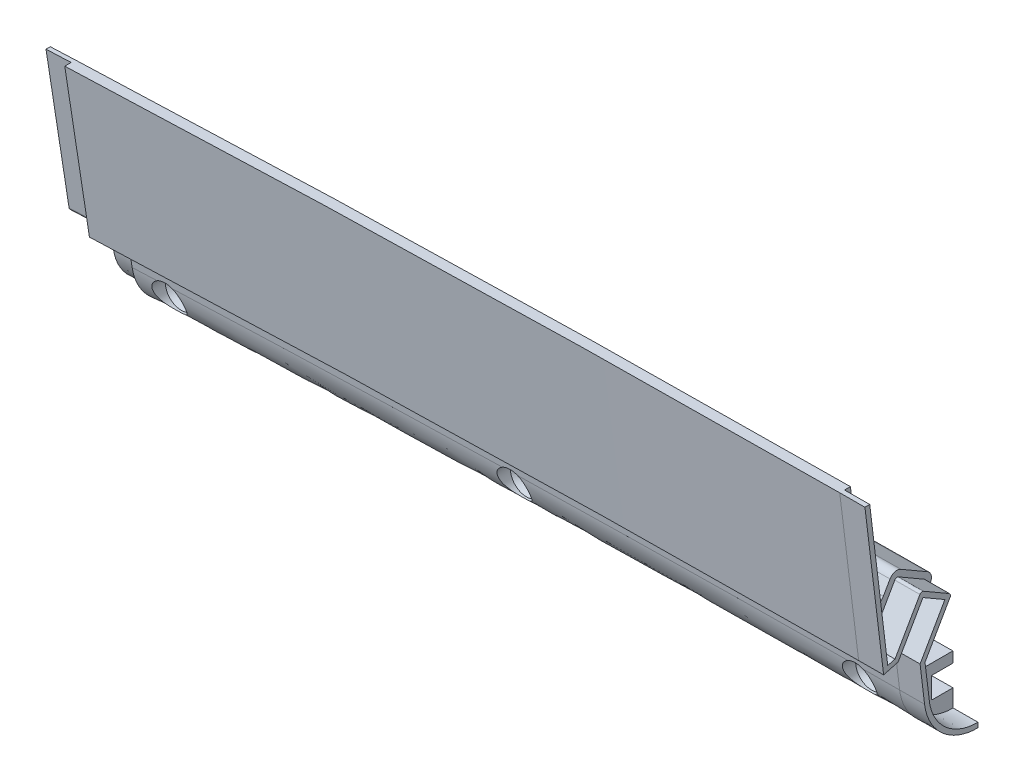
SolidWorks part; units mm, degrees
ref_plane "Front Plane" through (0, 0, 0) normal (0, 0, 1) x (1, 0, 0)
ref_plane "Top Plane" through (0, 0, 0) normal (0, 1, 0) x (1, 0, 0)
ref_plane "Right Plane" through (0, 0, 0) normal (1, 0, 0) x (0, 0, -1)
ref_plane "Plane3" through (-117.056, -3.871, 0) normal (0.9995, 0.0331, 0) x (0, 0, -1)
sketch "Sketch2" plane through (-117.056, -3.871, 0) normal (0.9995, 0.0331, 0) x (0, 0, -1)
  line L0 (-101.6, -41.1511) -> (-101.6, -45.9265)
  line L1 (-101.6, -41.1511) -> (-101.6, -45.9265)
  line L2 (-106.68, -45.9265) -> (-106.68, -50.6257)
  line L3 (-106.68, -45.9265) -> (-106.68, -50.6257)
  line L4 (-101.6, -50.6257) -> (-106.68, -50.6257)
  line L5 (-101.6, -50.6257) -> (-106.68, -50.6257)
  line L6 (-101.6, -50.6257) -> (-101.6, -56.1377)
  line L7 (-101.6, -50.6257) -> (-101.6, -56.1377)
  line L8 (-106.68, -45.9265) -> (-101.6, -45.9265)
  line L9 (-106.68, -45.9265) -> (-101.6, -45.9265)
  line L10 (-106.8705, -50.8162) -> (-108.9961, -53.9781) construction
  line L11 (-101.7905, -43.196) -> (-101.7905, -45.736)
  line L12 (-106.8705, -45.736) -> (-101.7905, -45.736)
  line L13 (-106.8705, -45.736) -> (-106.8705, -50.8162)
  line L14 (-101.7905, -50.8162) -> (-106.8705, -50.8162)
  line L15 (-101.7905, -50.8162) -> (-101.7905, -56.1377)
  line L16 (-101.7905, -43.196) -> (-101.6, -43.196)
  line L17 (-101.7905, -41.1511) -> (-101.7905, -45.736) construction
  line L18 (-120.8053, -33.0481) -> (-115.57, -36.0708)
  line L19 (-120.8053, -33.0481) -> (-115.57, -36.0708)
  line L20 (-109.601, -25.7318) -> (-114.8363, -22.709)
  line L21 (-109.601, -25.7318) -> (-114.8363, -22.709)
  line L22 (-114.8363, -22.709) -> (-120.8053, -33.0481)
  line L23 (-114.8363, -22.709) -> (-120.8053, -33.0481)
  line L24 (-115.57, -36.0708) -> (-109.601, -25.7318)
  line L25 (-115.57, -36.0708) -> (-109.601, -25.7318)
  line L26 (-115.57, -36.0708) -> (-114.523, -44.9291)
  line L28 (-118.1876, -34.5595) -> (-112.2186, -24.2204) construction
  line L29 (-114.6403, -39.5406) -> (-107.0838, -26.4518)
  line L30 (-107.7811, -23.8496) -> (-114.1162, -20.1918)
  line L31 (-116.7185, -20.8891) -> (-124.2749, -33.9778)
  line L33 (-106.1314, -24.8021) -> (-115.766, -19.2393) construction
  line L34 (-115.766, -19.2393) -> (-124.2749, -33.9778) construction
  line L35 (-114.6403, -39.5406) -> (-106.1314, -24.8021) construction
  line L36 (-124.2749, -33.9778) -> (-114.6403, -39.5406) construction
  line L37 (-112.9486, -36.6103) -> (-112.1701, -43.196)
  line L38 (-124.2749, -33.9778) -> (-128.0422, -2.1051)
  line L39 (-128.0422, -2.1051) -> (-132.6063, -0.4439)
  line L40 (-50.8, 0.7495) -> (-2184.4, 0.7495)
  line L41 (-125.822, 0.7495) -> (-133.442, 0.7495)
  line L42 (-122.1519, -30.3004) -> (-125.822, 0.7495)
  arc A0 (-114.523, -44.9291) -> (-101.7905, -56.1377) centre (-101.9108, -43.4383) ccw
  arc A2 (-114.1162, -20.1918) -> (-116.7185, -20.8891) centre (-115.0687, -21.8416) ccw
  arc A3 (-107.0838, -26.4518) -> (-107.7811, -23.8496) centre (-108.7336, -25.4993) ccw
  arc A4 (-133.442, 0.7495) -> (-132.6063, -0.4439) centre (-132.172, 0.7495) ccw
  point P41 (-133.442, 0.7495)
  dimension "D2" = 25.4
  dimension "D6" = 1.905
  dimension "D8" = 2.54
  dimension "D4" = 2.54
  dimension "D5" = 2.54
  dimension "D7" = 2.54
  dimension "D9" = 2.54
  dimension "D10" = 20
  dimension "D11" = 7.62
  dimension "D12" = 3.81
  dimension "D3" = 0.1905
sketch "Sketch3" plane through (0, 0, 101.6) normal (0, 0, 1) x (1, 0, 0)
  arc A0 (622.1039, -83.1998) -> (-622.1039, -83.1998) centre (0, -4954.4862) ccw construction
  arc A1 (622.1039, -83.1998) -> (-622.1039, -83.1998) centre (0, -4954.4862) ccw
sketch "Sketch4" plane through (-117.3306, 4.4304, 1117.6) normal (0.9995, 0.0331, 0) x (0, 0, -1)
  line L29 (1009.8189, -32.1556) -> (1003.4838, -28.4978) construction
  line L32 (1000.8815, -29.1951) -> (993.3251, -42.2838) construction
  line L35 (993.3251, -42.2838) -> (989.5578, -10.4111) construction
  line L50 (995.4481, -38.6064) -> (991.778, -7.5565) construction
  line L51 (1002.03, -44.3768) -> (1003.077, -53.235) construction
  line L52 (1015.8095, -59.1222) -> (1015.8095, -64.4437) construction
  line L53 (1015.8095, -59.1222) -> (1010.7295, -59.1222) construction
  line L54 (1010.7295, -54.042) -> (1010.7295, -59.1222) construction
  line L55 (1010.7295, -54.042) -> (1015.8095, -54.042) construction
  line L56 (1015.8095, -51.502) -> (1015.8095, -54.042) construction
  line L57 (1015.8095, -51.502) -> (1016, -51.502) construction
  line L58 (1004.6514, -44.9163) -> (1005.4299, -51.502) construction
  line L60 (1002.7637, -31.015) -> (996.7947, -41.3541) construction
  line L61 (1007.999, -34.0377) -> (1002.7637, -31.015) construction
  line L62 (1002.03, -44.3768) -> (1007.999, -34.0377) construction
  line L64 (991.5295, -5.4538) -> (988.9718, -5.4538)
  line L69 (1009.8189, -32.1556) -> (1003.4838, -28.4978)
  line L70 (1000.8815, -29.1951) -> (999.2724, -31.9822)
  line L71 (993.3251, -42.2838) -> (988.9718, -5.4538)
  line L74 (994.5502, -31.0104) -> (991.5295, -5.4538)
  line L75 (1002.03, -44.3768) -> (1003.077, -53.235)
  line L76 (1015.8095, -59.1222) -> (1015.8095, -64.4437)
  line L77 (1015.8095, -59.1222) -> (1010.7295, -59.1222)
  line L78 (1010.7295, -54.042) -> (1010.7295, -59.1222)
  line L79 (1010.7295, -54.042) -> (1015.8095, -54.042)
  line L80 (1015.8095, -51.502) -> (1015.8095, -54.042)
  line L81 (1015.8095, -51.502) -> (1007.6873, -51.502)
  line L82 (1004.7505, -45.7539) -> (1005.1649, -49.2601)
  line L84 (1002.7637, -31.015) -> (996.7947, -41.3541)
  line L85 (1007.999, -34.0377) -> (1002.7637, -31.015)
  line L86 (1002.03, -44.3768) -> (1007.999, -34.0377)
  line L87 (996.7947, -41.3541) -> (993.3251, -42.2838)
  line L88 (1005.0732, -44.1858) -> (1010.5162, -34.7578)
  arc A8 (1010.5162, -34.7578) -> (1009.8189, -32.1556) centre (1008.8664, -33.8053) ccw construction
  arc A9 (1003.4838, -28.4978) -> (1000.8815, -29.1951) centre (1002.5313, -30.1476) ccw construction
  arc A11 (1003.077, -53.235) -> (1015.8095, -64.4437) centre (1015.6892, -51.7443) ccw construction
  arc A12 (1010.5162, -34.7578) -> (1009.8189, -32.1556) centre (1008.8664, -33.8053) ccw
  arc A13 (1003.4838, -28.4978) -> (1000.8815, -29.1951) centre (1002.5313, -30.1476) ccw
  arc A15 (1003.077, -53.235) -> (1015.8095, -64.4437) centre (1015.6892, -51.7443) ccw
  arc A16 (1005.1649, -49.2601) -> (1007.6873, -51.502) centre (1007.6873, -48.962) ccw
  arc A17 (1004.7505, -45.7539) -> (1005.0732, -44.1858) centre (1007.2729, -45.4558) cw
  arc A18 (994.5502, -31.0104) -> (999.2724, -31.9822) centre (997.0727, -30.7122) ccw
  dimension "D2" = 2.54
  dimension "D1" = 36.83
sweep "Sweep3" add profiles "Sketch4" path "Sketch3"
sketch "Sketch5" plane through (0, 0, 101.7905) normal (0, 0, -1) x (-1, 0, 0)
  line L0 (207.2142, -20.037) -> (0, -4954.4862) construction
  line L1 (0, -4954.4862) -> (22.6014, 0.3132) construction
  line L2 (117.0808, -1.0187) -> (0, -4954.4862) construction
  arc A1 (628.0925, -39.606) -> (-627.2635, -39.5001) centre (0, -4954.4862) ccw construction
  point P2 (0, 0)
  point P4 (206.8956, -9.432)
  point P16 (117.0808, -1.0187)
ref_plane "Plane1" through (-207.6894, -8.7216, 0) normal (-0.9991, -0.042, 0) x (0.042, -0.9991, 0)
ref_plane "Plane2" through (-22.5995, -0.1031, 0) normal (1, 0.0046, 0) x (-0.0046, 1, 0)
other "SurfaceCut1"
other "SurfaceCut2"
sketch "Sketch8" plane through (-117.056, -3.871, 0) normal (0.9995, 0.0331, 0) x (0, 0, -1)
  line L0 (-106.8705, -50.8162) -> (-106.8705, -45.736)
  line L1 (-106.8705, -50.8162) -> (-106.8705, -45.736)
  line L2 (-106.8705, -48.2761) -> (-119.5705, -48.2761)
  line L3 (-119.5705, -48.2761) -> (-119.5705, -44.4661)
  line L4 (-119.5705, -44.4661) -> (-110.6805, -44.4661)
  line L5 (-110.6805, -44.4661) -> (-108.7755, -46.3711)
  line L6 (-108.7755, -46.3711) -> (-106.8705, -46.3711)
  line L7 (-119.5705, -48.2761) -> (-117.7248, -48.2761) construction
  dimension "D1" = 1.905
  dimension "D2" = 1.905
  dimension "D3" = 12.7
  dimension "D4" = 45
  dimension "D5" = 3.81
revolve "Cut-Revolve1" cut sketch "Sketch8" angle 360 about L7
sketch "Sketch9" plane through (0, 0, 106.8705) normal (0, 0, -1) x (-1, 0, 0)
  line L0 (198.0737, -52.2212) -> (197.8686, -57.297) construction
  line L1 (32.934, -48.3318) -> (32.8999, -53.4117) construction
  arc A1 (205.8492, -52.5415) -> (22.3798, -48.2723) centre (0, -4954.4862) ccw construction
  arc A2 (205.6361, -57.617) -> (22.3566, -53.3522) centre (0, -4954.4862) ccw construction
  point P8 (197.9712, -54.7591)
  point P11 (0, -4954.4862)
  point P16 (115.4604, -52.1207)
  dimension "D1" = 82.55
  dimension "D2" = 82.55
sketch "Sketch10" plane through (0, 0, 106.8705) normal (0, 0, -1) x (-1, 0, 0)
  line L0 (32.934, -48.3318) -> (32.8999, -53.4117) construction
  point P0 (32.917, -50.8717)
  point P1 (197.9712, -54.7591)
pattern_sketch "Sketch-Pattern1" of "Cut-Revolve1" driven by "Sketch10"
sketch "Sketch12" plane through (0, 0, 101.7905) normal (0, 0, -1) x (-1, 0, 0)
  line L0 (22.3914, -45.7325) -> (0, -4954.4862) construction
  line L1 (0, -4954.4862) -> (16.4224, -45.7089) construction
  arc A1 (205.9558, -50.0039) -> (22.3914, -45.7325) centre (0, -4954.4862) ccw construction
  arc A2 (22.3914, -45.7325) -> (16.4224, -45.7089) centre (0, -4954.4862) ccw
  dimension "D1" = 5.969
sketch "Sketch11" plane through (-22.5995, -0.1031, 0) normal (1, 0.0046, 0) x (0, 0, -1)
  line L0 (-127.4772, 0.4163) -> (-123.2949, -34.9662)
  line L1 (-123.2949, -34.9662) -> (-121.5584, -34.5009)
  line L2 (-121.5584, -34.5009) -> (-115.5722, -24.1324)
  line L3 (-114.7047, -23.8999) -> (-108.5896, -27.4305)
  line L4 (-108.3571, -28.298) -> (-114.3903, -38.7478)
  line L5 (-114.3903, -38.7478) -> (-113.3879, -47.2287)
  line L6 (-127.4931, 0.5505) -> (-123.2949, -34.9662) construction
  line L7 (-101.7905, -58.571) -> (-101.7905, -57.4281)
  line L8 (-101.7905, -53.2497) -> (-101.7905, -58.571) construction
  line L9 (-101.7905, -57.4281) -> (-101.8013, -57.4281)
  line L10 (-115.2547, -23.5824) -> (-108.0396, -27.748) construction
  line L11 (-108.0396, -27.748) -> (-114.3903, -38.7478) construction
  line L12 (-121.5584, -34.5009) -> (-115.2547, -23.5824) construction
  line L18 (-126.0705, 0.4163) -> (-128.6282, 0.4163)
  line L19 (-128.6282, 0.4163) -> (-124.2749, -36.4121)
  line L20 (-124.2749, -36.4121) -> (-120.8053, -35.4824)
  line L21 (-120.8053, -35.4824) -> (-114.8363, -25.1438)
  line L22 (-114.8363, -25.1438) -> (-109.601, -28.1664)
  line L23 (-109.601, -28.1664) -> (-115.57, -38.505)
  line L24 (-115.57, -38.505) -> (-114.523, -47.3628)
  line L25 (-101.7905, -58.571) -> (-101.7905, -53.2497)
  line L26 (-101.7905, -53.2497) -> (-106.8705, -53.2497)
  line L27 (-106.8705, -53.2497) -> (-106.8705, -48.1697)
  line L28 (-106.8705, -48.1697) -> (-101.7905, -48.1697)
  line L29 (-101.7905, -48.1697) -> (-101.7905, -45.6298)
  line L30 (-101.7905, -45.6298) -> (-109.9127, -45.6298)
  line L31 (-112.4351, -43.388) -> (-112.8495, -39.8821)
  line L32 (-112.5268, -38.314) -> (-107.0838, -28.8864)
  line L33 (-107.781, -26.2843) -> (-114.1162, -22.6267)
  line L34 (-116.7185, -23.324) -> (-118.3276, -26.111)
  line L35 (-123.0498, -25.1392) -> (-126.0705, 0.4163)
  line L36 (-127.4772, 0.4163) -> (-128.6282, 0.4163)
  line L37 (-128.6282, 0.4163) -> (-124.2749, -36.4121)
  line L38 (-124.2749, -36.4121) -> (-120.8053, -35.4824)
  line L39 (-120.8053, -35.4824) -> (-114.8363, -25.1438)
  line L40 (-114.8363, -25.1438) -> (-109.601, -28.1664)
  line L41 (-109.601, -28.1664) -> (-115.57, -38.505)
  line L42 (-115.57, -38.505) -> (-114.523, -47.3628)
  arc A0 (-108.5896, -27.4305) -> (-108.3571, -28.298) centre (-108.9071, -27.9805) cw
  arc A1 (-115.5722, -24.1324) -> (-114.7047, -23.8999) centre (-115.0222, -24.4499) cw
  arc A4 (-112.4351, -43.388) -> (-109.9127, -45.6298) centre (-109.9127, -43.0899) ccw
  arc A5 (-112.5268, -38.314) -> (-112.8495, -39.8821) centre (-110.3273, -39.5839) ccw
  arc A6 (-107.0838, -28.8864) -> (-107.781, -26.2843) centre (-108.7335, -27.934) ccw
  arc A7 (-114.1162, -22.6267) -> (-116.7185, -23.324) centre (-115.0687, -24.2765) ccw
  spline S0 degree 1 poles (-113.3879, -47.2287) (-101.8013, -57.4281) knots 0 0 1 1 construction
  spline S1 degree 3 poles (-113.3879, -47.2287) (-113.3048, -47.9315) (-113.0054, -49.3314) (-111.9316, -51.9222) (-109.7159, -54.7457) (-106.0351, -56.9465) (-103.2019, -57.4413) (-101.8013, -57.4281) knots 0 0 0 0 0.125 0.25 0.5 0.75 1 1 1 1
  spline S2 degree 3 poles (1806.7112, 500.659) (415.3182, 185.4234) (-128.7728, 19.3052) (-114.2511, -48.8982) (-114.1523, -49.2756) (-113.8076, -50.3834) (-113.513, -51.0946) (-112.7943, -52.4623) (-112.3662, -53.1223) (-111.4114, -54.3348) (-110.8822, -54.8941) (-110.0099, -55.6617) (-109.7043, -55.9068) (-109.0766, -56.3642) (-108.7542, -56.5771) (-107.762, -57.1697) (-107.0674, -57.5036) (-105.9744, -57.9102) (-105.6018, -58.0296) (-104.8546, -58.2318) (-104.4782, -58.3153) (-51.6561, -67.5546) (53.4105, 250.997) (369.459, 1883.482) knots -11.048432 -11.048432 -11.048432 -11.048432 0.0625 0.0625 0.125 0.125 0.25 0.25 0.375 0.375 0.5 0.5 0.5625 0.5625 0.625 0.625 0.75 0.75 0.8125 0.8125 0.875 0.875 9.519326 9.519326 9.519326 9.519326 only from (-114.523, -47.3628) to (-101.7905, -58.571)
  spline S3 degree 3 poles (-966.8365, -555.2864) (-146.5253, 43.3441) (-110.7563, -19.4511) (-119.0219, -26.9036) (-119.2485, -27.0513) (-119.7291, -27.2666) (-119.9898, -27.3374) (-120.3827, -27.3802) (-120.5144, -27.3844) (-120.779, -27.3719) (-120.9121, -27.3551) (-121.1705, -27.3017) (-121.297, -27.2651) (-121.5443, -27.1722) (-121.6661, -27.1152) (-121.896, -26.9847) (-122.0051, -26.911) (-122.2115, -26.7469) (-122.3097, -26.6555) (-122.5785, -26.3624) (-122.7254, -26.1414) (-131.5662, -6.8591) (104.7841, 84.3421) (817.0787, 315.6785) knots -5.03449 -5.03449 -5.03449 -5.03449 0.125 0.125 0.25 0.25 0.375 0.375 0.4375 0.4375 0.5 0.5 0.5625 0.5625 0.625 0.625 0.6875 0.6875 0.75 0.75 0.875 0.875 10.718854 10.718854 10.718854 10.718854 only from (-118.3276, -26.111) to (-123.0498, -25.1392)
  spline S4 degree 3 poles (-114.523, -47.3628) (-114.4771, -47.7506) (-114.4136, -48.1352) (-114.2511, -48.8982) (-114.1523, -49.2756) (-113.8076, -50.3834) (-113.513, -51.0946) (-112.7943, -52.4623) (-112.3662, -53.1223) (-111.4114, -54.3348) (-110.8822, -54.8941) (-110.0099, -55.6617) (-109.7043, -55.9068) (-109.0766, -56.3642) (-108.7542, -56.5771) (-107.762, -57.1697) (-107.0674, -57.5036) (-105.9744, -57.9102) (-105.6018, -58.0296) (-104.8546, -58.2318) (-104.4782, -58.3153) (-103.3407, -58.5143) (-102.5713, -58.5784) (-101.7905, -58.571) knots 0 0 0 0 0.0625 0.0625 0.125 0.125 0.25 0.25 0.375 0.375 0.5 0.5 0.5625 0.5625 0.625 0.625 0.75 0.75 0.8125 0.8125 0.875 0.875 1 1 1 1
  dimension "D3" = 0.635
  dimension "D1" = 0
  dimension "D2" = 1.143
sweep "Sweep4" add profiles "Sketch11" path "Sketch12"
sketch "Sketch14" plane through (-207.6894, -8.7216, 0) normal (-0.9991, -0.042, 0) x (0, 0, 1)
  line L0 (113.0095, -42.8728) -> (113.9971, -34.5176)
  line L1 (113.9971, -34.5176) -> (107.5192, -23.2974)
  line L2 (107.5192, -23.2974) -> (115.3941, -18.7508)
  line L3 (115.3941, -18.7508) -> (121.8095, -29.8626)
  line L4 (121.8095, -29.8626) -> (122.9682, -30.173)
  line L5 (122.9682, -30.173) -> (127.1147, 4.9064)
  line L18 (128.6282, 4.7275) -> (126.0705, 4.7275)
  line L19 (126.0705, 4.7275) -> (123.0498, -20.828)
  line L20 (118.3276, -21.7998) -> (116.7185, -19.0128)
  line L21 (114.1162, -18.3156) -> (107.7811, -21.9731)
  line L22 (107.0838, -24.5753) -> (112.5268, -34.0029)
  line L23 (112.8495, -35.5709) -> (112.4351, -39.0769)
  line L24 (109.9127, -41.3187) -> (101.7905, -41.3187)
  line L25 (101.7905, -41.3187) -> (101.7905, -43.8586)
  line L26 (101.7905, -43.8586) -> (106.8705, -43.8586)
  line L27 (106.8705, -43.8586) -> (106.8705, -48.9385)
  line L28 (106.8705, -48.9385) -> (101.7905, -48.9385)
  line L29 (101.7905, -48.9385) -> (101.7905, -54.2599)
  line L30 (114.523, -43.0517) -> (115.57, -34.1939)
  line L31 (115.57, -34.1939) -> (109.601, -23.8552)
  line L32 (109.601, -23.8552) -> (114.8363, -20.8326)
  line L33 (114.8363, -20.8326) -> (120.8053, -31.1713)
  line L34 (120.8053, -31.1713) -> (124.2749, -32.1009)
  line L35 (124.2749, -32.1009) -> (128.6282, 4.7275)
  line L36 (128.6282, 4.7275) -> (126.0705, 4.7275)
  line L37 (126.0705, 4.7275) -> (123.0498, -20.828)
  line L38 (118.3276, -21.7998) -> (116.7185, -19.0128)
  line L39 (114.1162, -18.3156) -> (107.7811, -21.9731)
  line L40 (107.0838, -24.5753) -> (112.5268, -34.0029)
  line L41 (112.8495, -35.5709) -> (112.4351, -39.0769)
  line L42 (109.9127, -41.3187) -> (101.7905, -41.3187)
  line L43 (101.7905, -41.3187) -> (101.7905, -43.8586)
  line L44 (101.7905, -43.8586) -> (106.8705, -43.8586)
  line L45 (106.8705, -43.8586) -> (106.8705, -48.9385)
  line L46 (106.8705, -48.9385) -> (101.7905, -48.9385)
  line L47 (101.7905, -48.9385) -> (101.7905, -54.2599)
  line L48 (114.523, -43.0517) -> (115.57, -34.1939)
  line L49 (115.57, -34.1939) -> (109.601, -23.8552)
  line L50 (109.601, -23.8552) -> (114.8363, -20.8326)
  line L51 (114.8363, -20.8326) -> (120.8053, -31.1713)
  line L52 (120.8053, -31.1713) -> (124.2749, -32.1009)
  line L53 (124.2749, -32.1009) -> (128.6282, 4.7275)
  arc A4 (116.7185, -19.0128) -> (114.1162, -18.3156) centre (115.0687, -19.9654) ccw
  arc A5 (107.7811, -21.9731) -> (107.0838, -24.5753) centre (108.7335, -23.6228) ccw
  arc A6 (112.8495, -35.5709) -> (112.5268, -34.0029) centre (110.3273, -35.2728) ccw
  arc A7 (109.9127, -41.3187) -> (112.4351, -39.0769) centre (109.9127, -38.7787) ccw
  arc A8 (116.7185, -19.0128) -> (114.1162, -18.3156) centre (115.0687, -19.9654) ccw
  arc A9 (107.7811, -21.9731) -> (107.0838, -24.5753) centre (108.7335, -23.6228) ccw
  arc A10 (112.8495, -35.5709) -> (112.5268, -34.0029) centre (110.3273, -35.2728) ccw
  arc A11 (109.9127, -41.3187) -> (112.4351, -39.0769) centre (109.9127, -38.7787) ccw
  spline S0 degree 1 poles (101.8049, -52.7359) (113.0095, -42.8728) knots 0 0 1 1 construction
  spline S1 degree 3 poles (101.8049, -52.7359) (102.4893, -52.7424) (103.8689, -52.6269) (106.4858, -51.9145) (109.4658, -50.1356) (112.0284, -46.8748) (112.8505, -44.2179) (113.0095, -42.8728) knots 0 0 0 0 0.125 0.25 0.5 0.75 1 1 1 1
  spline S2 degree 3 poles (-942.5282, -1710.9073) (36.0617, 56.3998) (128.5401, -9.1891) (122.7249, -21.8305) (122.575, -22.0556) (122.2185, -22.4431) (122.0069, -22.6111) (121.6628, -22.8057) (121.5435, -22.8614) (121.2955, -22.9545) (121.1665, -22.9916) (120.908, -23.0445) (120.7774, -23.0609) (120.5134, -23.0732) (120.3791, -23.0689) (120.1163, -23.0398) (119.987, -23.0151) (119.7325, -22.9458) (119.6063, -22.9006) (119.2436, -22.7375) (119.0214, -22.5924) (97.7555, -3.3699) (438.2034, 315.4392) (1602.9016, 1317.7063) knots -6.357152 -6.357152 -6.357152 -6.357152 0.125 0.125 0.25 0.25 0.375 0.375 0.4375 0.4375 0.5 0.5 0.5625 0.5625 0.625 0.625 0.6875 0.6875 0.75 0.75 0.875 0.875 14.22173 14.22173 14.22173 14.22173 only from (123.0498, -20.828) to (118.3276, -21.7998)
  spline S3 degree 3 poles (-198.2751, 1920.9429) (-61.9416, 500.6571) (33.8593, -59.9408) (103.3479, -54.1849) (103.7348, -54.1347) (104.8774, -53.9333) (105.6202, -53.7312) (107.068, -53.1919) (107.777, -52.8509) (109.1008, -52.0576) (109.7227, -51.6036) (110.5948, -50.8357) (110.8766, -50.5636) (111.4099, -49.999) (111.662, -49.7063) (112.3757, -48.7973) (112.795, -48.1506) (113.3369, -47.118) (113.5026, -46.7635) (113.7979, -46.048) (113.9285, -45.6853) (129.7895, 5.5325) (-172.8299, 150.1214) (-1752.0895, 670.5998) knots -11.047615 -11.047615 -11.047615 -11.047615 0.0625 0.0625 0.125 0.125 0.25 0.25 0.375 0.375 0.5 0.5 0.5625 0.5625 0.625 0.625 0.75 0.75 0.8125 0.8125 0.875 0.875 9.518256 9.518256 9.518256 9.518256 only from (101.7905, -54.2599) to (114.523, -43.0517)
  spline S4 degree 3 poles (123.0498, -20.828) (123.0184, -21.0932) (122.9449, -21.3522) (122.7249, -21.8305) (122.575, -22.0556) (122.2185, -22.4431) (122.0069, -22.6111) (121.6628, -22.8057) (121.5435, -22.8614) (121.2955, -22.9545) (121.1665, -22.9916) (120.908, -23.0445) (120.7774, -23.0609) (120.5134, -23.0732) (120.3791, -23.0689) (120.1163, -23.0398) (119.987, -23.0151) (119.7325, -22.9458) (119.6063, -22.9006) (119.2436, -22.7375) (119.0214, -22.5924) (118.6267, -22.2357) (118.4611, -22.031) (118.3276, -21.7998) knots 0 0 0 0 0.125 0.125 0.25 0.25 0.375 0.375 0.4375 0.4375 0.5 0.5 0.5625 0.5625 0.625 0.625 0.6875 0.6875 0.75 0.75 0.875 0.875 1 1 1 1
  spline S5 degree 3 poles (101.7905, -54.2599) (102.1809, -54.2636) (102.5705, -54.2493) (103.3479, -54.1849) (103.7348, -54.1347) (104.8774, -53.9333) (105.6202, -53.7312) (107.068, -53.1919) (107.777, -52.8509) (109.1008, -52.0576) (109.7227, -51.6036) (110.5948, -50.8357) (110.8766, -50.5636) (111.4099, -49.999) (111.662, -49.7063) (112.3757, -48.7973) (112.795, -48.1506) (113.3369, -47.118) (113.5026, -46.7635) (113.7979, -46.048) (113.9285, -45.6853) (114.2702, -44.5822) (114.4313, -43.8271) (114.523, -43.0517) knots 0 0 0 0 0.0625 0.0625 0.125 0.125 0.25 0.25 0.375 0.375 0.5 0.5 0.5625 0.5625 0.625 0.625 0.75 0.75 0.8125 0.8125 0.875 0.875 1 1 1 1
  dimension "D1" = 0
  dimension "D2" = 1.524
sketch "Sketch15" plane through (-207.6894, -8.7216, 0) normal (-0.9991, -0.042, 0) x (0, 0, 1)
  line L0 (113.0095, -42.8728) -> (113.9971, -34.5176) construction
  line L1 (113.9971, -34.5176) -> (107.5192, -23.2974) construction
  line L2 (107.5192, -23.2974) -> (115.3941, -18.7508) construction
  line L3 (115.3941, -18.7508) -> (121.8095, -29.8626) construction
  line L4 (121.8095, -29.8626) -> (122.9682, -30.173) construction
  line L5 (122.9682, -30.173) -> (127.1147, 4.9064) construction
  line L6 (113.0095, -42.8728) -> (113.9724, -34.727)
  line L7 (113.8917, -34.3349) -> (107.5192, -23.2974)
  line L8 (107.5192, -23.2974) -> (115.3941, -18.7508)
  line L9 (115.3941, -18.7508) -> (121.678, -29.6348)
  line L10 (122.0636, -29.9306) -> (122.2594, -29.9831)
  line L11 (123.0543, -29.4443) -> (127.0936, 4.7275)
  line L12 (101.7905, -48.9385) -> (101.7905, -54.2599) construction
  line L13 (101.7905, -48.9385) -> (101.7905, -52.7359)
  line L14 (101.8049, -52.7359) -> (101.7905, -52.7359)
  line L18 (124.2749, -32.1009) -> (128.6282, 4.7275)
  line L19 (128.6282, 4.7275) -> (126.0705, 4.7275)
  line L20 (126.0705, 4.7275) -> (123.0498, -20.828)
  line L21 (118.3276, -21.7998) -> (116.7185, -19.0128)
  line L22 (114.1162, -18.3156) -> (107.7811, -21.9731)
  line L23 (107.0838, -24.5753) -> (112.5268, -34.0029)
  line L24 (112.8495, -35.5709) -> (112.4351, -39.0769)
  line L25 (109.9127, -41.3187) -> (101.7905, -41.3187)
  line L26 (101.7905, -41.3187) -> (101.7905, -43.8586)
  line L27 (101.7905, -43.8586) -> (106.8705, -43.8586)
  line L28 (106.8705, -43.8586) -> (106.8705, -48.9385)
  line L29 (106.8705, -48.9385) -> (101.7905, -48.9385)
  line L30 (101.7905, -48.9385) -> (101.7905, -54.2599)
  line L31 (114.523, -43.0517) -> (115.57, -34.1939)
  line L32 (115.57, -34.1939) -> (109.601, -23.8552)
  line L33 (109.601, -23.8552) -> (114.8363, -20.8326)
  line L34 (114.8363, -20.8326) -> (120.8053, -31.1713)
  line L35 (120.8053, -31.1713) -> (124.2749, -32.1009)
  line L37 (127.0936, 4.7275) -> (126.0705, 4.7275)
  line L38 (126.0705, 4.7275) -> (123.0498, -20.828)
  line L39 (118.3276, -21.7998) -> (116.7185, -19.0128)
  line L40 (114.1162, -18.3156) -> (107.7811, -21.9731)
  line L41 (107.0838, -24.5753) -> (112.5268, -34.0029)
  line L42 (112.8495, -35.5709) -> (112.4351, -39.0769)
  line L43 (109.9127, -41.3187) -> (101.7905, -41.3187)
  line L44 (101.7905, -41.3187) -> (101.7905, -43.8586)
  line L45 (101.7905, -43.8586) -> (106.8705, -43.8586)
  line L46 (106.8705, -43.8586) -> (106.8705, -48.9385)
  line L47 (106.8705, -48.9385) -> (101.7905, -48.9385)
  arc A0 (113.9724, -34.727) -> (113.8917, -34.3349) centre (113.3418, -34.6524) ccw
  arc A1 (121.678, -29.6348) -> (122.0636, -29.9306) centre (122.2279, -29.3173) ccw
  arc A2 (122.2594, -29.9831) -> (123.0543, -29.4443) centre (122.4237, -29.3697) ccw
  arc A4 (116.7185, -19.0128) -> (114.1162, -18.3156) centre (115.0687, -19.9654) ccw
  arc A5 (107.7811, -21.9731) -> (107.0838, -24.5753) centre (108.7335, -23.6228) ccw
  arc A6 (112.8495, -35.5709) -> (112.5268, -34.0029) centre (110.3273, -35.2728) ccw
  arc A7 (109.9127, -41.3187) -> (112.4351, -39.0769) centre (109.9127, -38.7787) ccw
  arc A8 (116.7185, -19.0128) -> (114.1162, -18.3156) centre (115.0687, -19.9654) ccw
  arc A9 (107.7811, -21.9731) -> (107.0838, -24.5753) centre (108.7335, -23.6228) ccw
  arc A10 (112.8495, -35.5709) -> (112.5268, -34.0029) centre (110.3273, -35.2728) ccw
  arc A11 (109.9127, -41.3187) -> (112.4351, -39.0769) centre (109.9127, -38.7787) ccw
  spline S0 degree 3 poles (1017.1764, 349.8617) (33.3195, 15.4991) (81.1965, -58.7983) (106.4858, -51.9145) (109.4658, -50.1356) (129.6733, -24.4226) (35.2847, 62.2004) (-468.3002, -856.541) knots -4.331915 -4.331915 -4.331915 -4.331915 0.125 0.25 0.5 0.75 6.164151 6.164151 6.164151 6.164151 only from (101.8049, -52.7359) to (113.0095, -42.8728) construction
  spline S1 degree 3 poles (101.8049, -52.7359) (102.4893, -52.7424) (103.8689, -52.6269) (106.4858, -51.9145) (109.4658, -50.1356) (112.0284, -46.8748) (112.8505, -44.2179) (113.0095, -42.8728) knots 0 0 0 0 0.125 0.25 0.5 0.75 1 1 1 1
  spline S2 degree 3 poles (-942.5282, -1710.9073) (36.0617, 56.3998) (128.5401, -9.1891) (122.7249, -21.8305) (122.575, -22.0556) (122.2185, -22.4431) (122.0069, -22.6111) (121.6628, -22.8057) (121.5435, -22.8614) (121.2955, -22.9545) (121.1665, -22.9916) (120.908, -23.0445) (120.7774, -23.0609) (120.5134, -23.0732) (120.3791, -23.0689) (120.1163, -23.0398) (119.987, -23.0151) (119.7325, -22.9458) (119.6063, -22.9006) (119.2436, -22.7375) (119.0214, -22.5924) (97.7555, -3.3699) (438.2034, 315.4392) (1602.9016, 1317.7063) knots -6.357152 -6.357152 -6.357152 -6.357152 0.125 0.125 0.25 0.25 0.375 0.375 0.4375 0.4375 0.5 0.5 0.5625 0.5625 0.625 0.625 0.6875 0.6875 0.75 0.75 0.875 0.875 14.22173 14.22173 14.22173 14.22173 only from (123.0498, -20.828) to (118.3276, -21.7998)
  spline S3 degree 3 poles (-93.3253, 926.519) (-10.5613, 231.9181) (53.1389, -58.3439) (103.3479, -54.1849) (103.7348, -54.1347) (104.8774, -53.9333) (105.6202, -53.7312) (107.068, -53.1919) (107.777, -52.8509) (109.1008, -52.0576) (109.7227, -51.6036) (110.5948, -50.8357) (110.8766, -50.5636) (111.4099, -49.999) (111.662, -49.7063) (112.3757, -48.7973) (112.795, -48.1506) (113.3369, -47.118) (113.5026, -46.7635) (113.7979, -46.048) (113.9285, -45.6853) (125.9187, -6.967) (-43.2917, 84.7021) (-804.6708, 350.7273) knots -7.947776 -7.947776 -7.947776 -7.947776 0.0625 0.0625 0.125 0.125 0.25 0.25 0.375 0.375 0.5 0.5 0.5625 0.5625 0.625 0.625 0.75 0.75 0.8125 0.8125 0.875 0.875 7.39364 7.39364 7.39364 7.39364 only from (101.7905, -54.2599) to (114.523, -43.0517)
  spline S4 degree 3 poles (123.0498, -20.828) (123.0184, -21.0932) (122.9449, -21.3522) (122.7249, -21.8305) (122.575, -22.0556) (122.2185, -22.4431) (122.0069, -22.6111) (121.6628, -22.8057) (121.5435, -22.8614) (121.2955, -22.9545) (121.1665, -22.9916) (120.908, -23.0445) (120.7774, -23.0609) (120.5134, -23.0732) (120.3791, -23.0689) (120.1163, -23.0398) (119.987, -23.0151) (119.7325, -22.9458) (119.6063, -22.9006) (119.2436, -22.7375) (119.0214, -22.5924) (118.6267, -22.2357) (118.4611, -22.031) (118.3276, -21.7998) knots 0 0 0 0 0.125 0.125 0.25 0.25 0.375 0.375 0.4375 0.4375 0.5 0.5 0.5625 0.5625 0.625 0.625 0.6875 0.6875 0.75 0.75 0.875 0.875 1 1 1 1
  dimension "D2" = 0.635
  dimension "D1" = 0
sketch "Sketch16" plane through (0, 0, 101.7905) normal (0, 0, -1) x (-1, 0, 0)
  arc A0 (211.9194, -50.2579) -> (205.9558, -50.0039) centre (0, -4954.4862) ccw
  arc A1 (205.9558, -50.0039) -> (22.3914, -45.7325) centre (0, -4954.4862) ccw construction
  dimension "D1" = 5.969
sweep "Sweep5" add profiles "Sketch15" path "Sketch16"
